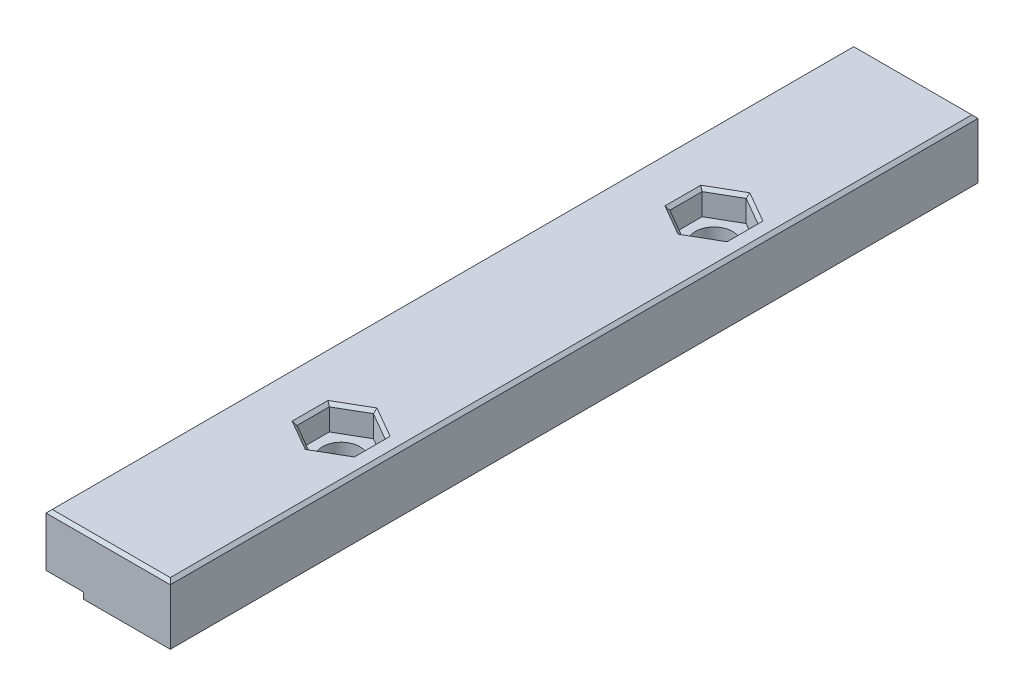
SolidWorks part; units mm, degrees
material "ABS"
ref_plane "Front Plane" through (0, 0, 0) normal (0, 0, 1) x (1, 0, 0)
ref_plane "Top Plane" through (0, 0, 0) normal (0, 1, 0) x (1, 0, 0)
ref_plane "Right Plane" through (0, 0, 0) normal (1, 0, 0) x (0, 0, -1)
sketch "Sketch1" plane through (0, 0, 0) normal (0, 0, 1) x (1, 0, 0)
  line L0 (20, 20.188) -> (0, 20.188)
  line L1 (0, 20.188) -> (0, 10.188)
  line L5 (20, 10.188) -> (20, 20.188)
  line L6 (0, 10.188) -> (20, 10.188)
  dimension "D1" = 20
  dimension "D2" = 10
  dimension "D3" = 10
extrude "Boss-Extrude1" add sketch "Sketch1" along normal blind 130
sketch "Sketch2" plane through (0, 20.188, 0) normal (0, 1, 0) x (1, 0, 0)
  line L0 (20, 0) -> (0, 0) construction
  line L1 (20, -130) -> (20, 0) construction
  circle A0 centre (12.5, -35) radius 3
  dimension "D1" = 35
  dimension "D2" = 7.5
extrude "Cut-Extrude1" cut sketch "Sketch2" against normal blind 140
sketch "Sketch3" plane through (0, 20.188, 0) normal (0, 1, 0) x (1, 0, 0)
  line L0 (20, -130) -> (20, 0) construction
  line L1 (12.5, -29.8038) -> (8, -32.4019)
  line L2 (8, -32.4019) -> (8, -37.5981)
  line L3 (8, -37.5981) -> (12.5, -40.1962)
  line L4 (12.5, -40.1962) -> (17, -37.5981)
  line L5 (17, -37.5981) -> (17, -32.4019)
  line L6 (17, -32.4019) -> (12.5, -29.8038)
  circle A0 centre (12.5, -35) radius 4.5 construction
  dimension "D1" = 9
extrude "Cut-Extrude2" cut sketch "Sketch3" against normal blind 4
pattern_linear "LPattern1" count 2 spacing 60 along (0, 0, 1) of "Cut-Extrude1", "Cut-Extrude2"
sketch "Sketch4" plane through (0, 0, 0) normal (0, 0, -1) x (-1, 0, 0)
  line L1 (0, 10.188) -> (-6, 10.188)
  line L2 (0, 10.188) -> (0, 11.688)
  line L3 (0, 11.688) -> (-6, 11.688)
  line L4 (-6, 10.188) -> (-6, 11.688)
  dimension "D1" = 1.5
  dimension "D2" = 6
extrude "Cut-Extrude3" cut sketch "Sketch4" against normal blind 200
chamfer "Chamfer1" distance 0.5 angle 45 22 edges at (20, 10.188, 65) (13, 10.188, 0) (6, 10.188, 65) (13, 10.188, 130) (9.5, 10.188, 35) (9.5, 10.188, 95) (20, 20.188, 65) (10, 20.188, 130) (0, 20.188, 65) (10, 20.188, 0) (8, 20.188, 35) (10.25, 20.188, 38.8971) (14.75, 20.188, 38.8971) (17, 20.188, 35) (14.75, 20.188, 31.1029) (10.25, 20.188, 31.1029) (8, 20.188, 95) (10.25, 20.188, 98.8971) (14.75, 20.188, 98.8971) (17, 20.188, 95) (14.75, 20.188, 91.1029) (10.25, 20.188, 91.1029)
